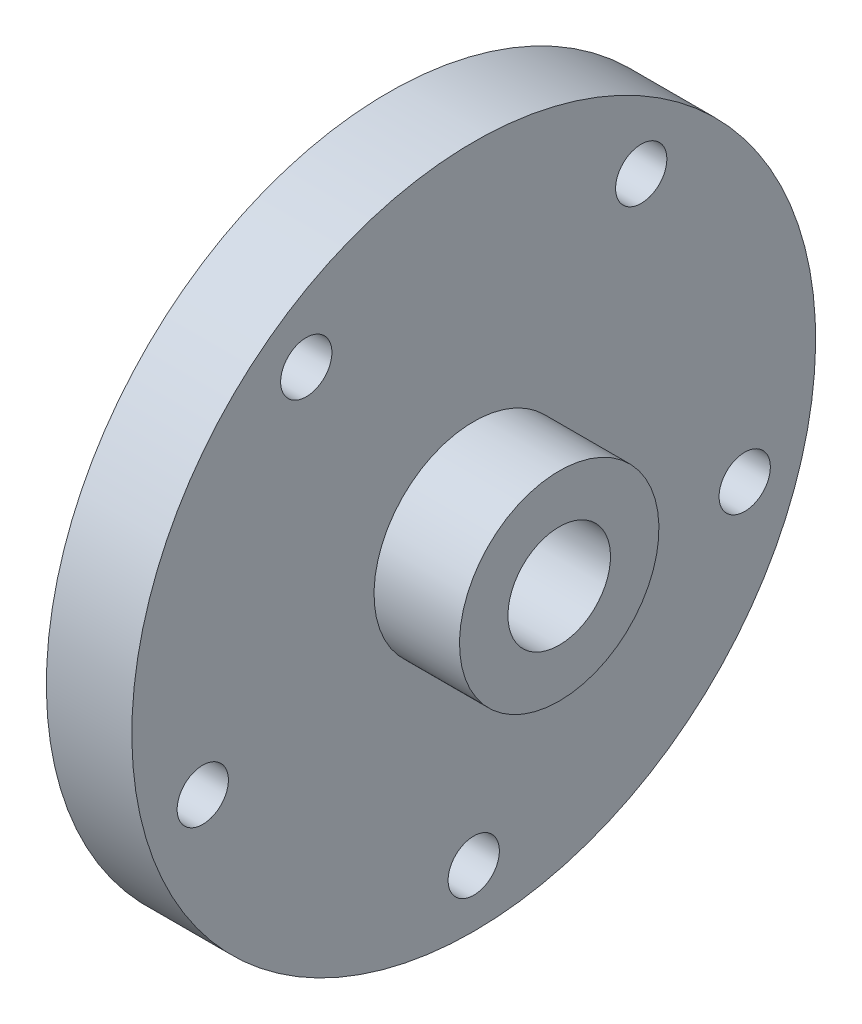
SolidWorks part; units mm, degrees
material "1.0037 (S235JR)"
ref_plane "Front Plane" through (0, 0, 0) normal (0, 0, 1) x (1, 0, 0)
ref_plane "Top Plane" through (0, 0, 0) normal (0, 1, 0) x (1, 0, 0)
ref_plane "Right Plane" through (0, 0, 0) normal (1, 0, 0) x (0, 0, -1)
sketch "Sketch2" plane through (0, 0, 0) normal (0, 0, 1) x (1, 0, 0)
  line L0 (-30, 0) -> (0, 0) construction
  line L1 (0, 0) -> (0, 17.5)
  line L2 (0, 17.5) -> (-15, 17.5)
  line L3 (-15, 17.5) -> (-15, 60)
  line L4 (-30, 12.5) -> (-20, 12.5)
  line L5 (-30, 12.5) -> (-30, 0)
  line L6 (-30, 9) -> (0, 9)
  line L7 (-20, 12.5) -> (-20, 37.5)
  line L8 (-20, 37.5) -> (-30, 37.5)
  line L9 (-30, 37.5) -> (-30, 60)
  line L10 (-30, 60) -> (-15, 60)
  dimension "D1" = 25
  dimension "D2" = 18
  dimension "D3" = 120
  dimension "D4" = 75
  dimension "D5" = 35
  dimension "D6" = 10
  dimension "D7" = 5
  dimension "D8" = 15
revolve "Revolve1" add sketch "Sketch2" angle 360 about L0
sketch "Sketch3" plane through (-15, 0, 0) normal (1, 0, 0) x (0, 0, -1)
  point P0 (0, -50)
  point P1 (0, 0)
  point P3 (0, 0)
  dimension "D1" = 50
hole_wizard "M8 Clearance Hole1" positions "3DSketch1" profile "Sketch4" hole size "M8" standard "ISO" end condition up to next
sketch3d "3DSketch1"
  point P0 (-15, -50, 0)
sketch "Sketch4" plane through (-15, -50, 0) normal (0, 1, 0) x (0, 0, -1)
  line L0 (0, 0) -> (0, 15)
  line L1 (0, 15) -> (4.5, 15)
  line L2 (4.5, 15) -> (4.5, 0)
  line L5 (4.5, 0) -> (0, 0)
  line L11 (0, -6.35) -> (0, 107.95) construction
  dimension "Thru Hole Dia." = 9
  dimension "Thru Hole Depth" = 15
pattern_circular "CirPattern1" count 5 over 360 about axis through (0, 0, 0) along (1, 0, 0) of "M8 Clearance Hole1"
